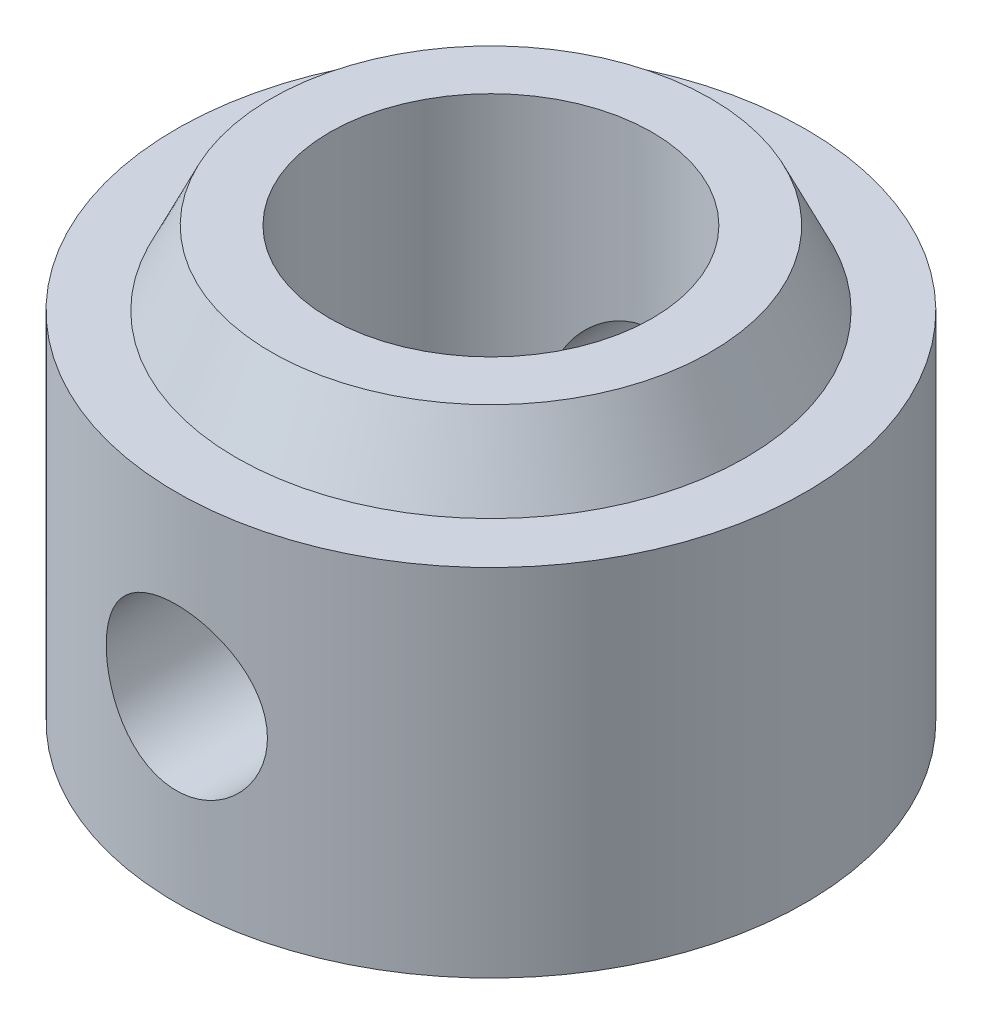
SolidWorks part; units mm, degrees
ref_plane "Front Plane" through (0, 0, 0) normal (0, 0, 1) x (1, 0, 0)
ref_plane "Top Plane" through (0, 0, 0) normal (0, 1, 0) x (1, 0, 0)
ref_plane "Right Plane" through (0, 0, 0) normal (1, 0, 0) x (0, 0, -1)
sketch "Sketch2" plane through (0, 0, 0) normal (0, 0, 1) x (1, 0, 0)
  line L0 (0, 0) -> (0, 6.1232) construction
  line L1 (2.05, 5.461) -> (2.05, 0)
  line L2 (2.05, 0) -> (4.0005, 0)
  line L3 (4.0005, 0) -> (4.0005, 4.5212)
  line L5 (4.0005, 4.5212) -> (3.2385, 4.5212)
  line L6 (2.794, 5.461) -> (2.05, 5.461)
  line L7 (3.2385, 4.5212) -> (2.794, 5.461)
  dimension "D1" = 4.1
  dimension "D2" = 8.001
  dimension "D3" = 5.461
  dimension "D4" = 4.5212
  dimension "D5" = 6.477
  dimension "D6" = 5.588
revolve "Revolve1" add sketch "Sketch2" angle 360 about L0
hole_wizard "M2.5x0.45 Tapped Hole1" positions "3DSketch1" profile "Sketch3" tap size "M2.5x0.45" standard "ANSI Metric" end condition through all
sketch3d "3DSketch1"
  line L0 (0, 4.5212, 4.0005) -> (0, 0, 4.0005) construction
  line L3 (0, 2.2606, 4.0005) -> (0, 2.2606, 0) construction
  line L5 (0, 2.2606, 0) -> (0, 0, 0) construction
  circle A0 centre (0, 4.5212, 0) radius 4.0005 construction
  circle A1 centre (0, 0, 0) radius 4.0005 construction
  point P0 (0, 2.2606, 4.0005)
  point P7 (0, 0.5207, 0)
  point P10 (0, -4.0005, 0)
sketch "Sketch3" plane through (0, 2.2606, 4.0005) normal (1, 0, 0) x (0, -1, 0)
  line L0 (0, 0) -> (0, 8.001)
  line L1 (0, 8.001) -> (1.025, 8.001)
  line L2 (1.025, 8.001) -> (1.025, 0)
  line L5 (1.025, 0) -> (0, 0)
  line L11 (0, -6.35) -> (0, 107.95) construction
  dimension "Thru Tap Drill Dia." = 2.05
  dimension "Thru Tap Drill Depth" = 8.001
cosmetic thread "Hole Thread1"
